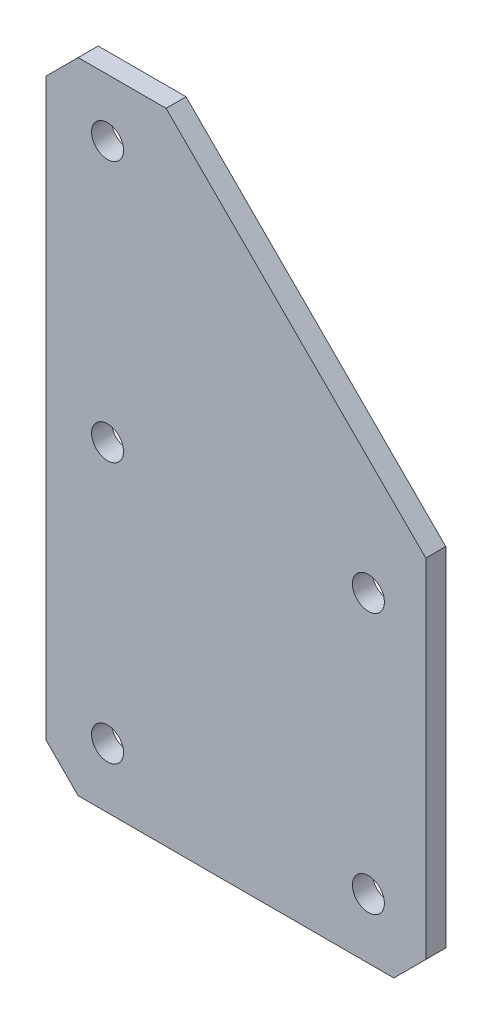
SolidWorks part; units mm, degrees
ref_plane "Front Plane" through (0, 0, 0) normal (0, 0, 1) x (1, 0, 0)
ref_plane "Top Plane" through (0, 0, 0) normal (0, 1, 0) x (1, 0, 0)
ref_plane "Right Plane" through (0, 0, 0) normal (1, 0, 0) x (0, 0, -1)
sketch "Sketch1" plane through (0, 0, 0) normal (0, 0, 1) x (1, 0, 0)
  line L0 (-95.3644, 10.476) -> (-35.0394, 10.476)
  line L3 (-35.0394, 70.801) -> (-35.0394, 10.476)
  line L4 (-95.3644, 112.076) -> (-95.3644, 10.476)
  line L5 (-95.3644, 112.076) -> (-76.3144, 112.076)
  line L6 (-35.0394, 70.801) -> (-76.3144, 112.076)
  dimension "D1" = 101.6
extrude "Boss-Extrude1" add sketch "Sketch1" along normal blind 3.175
sketch "Sketch2" plane through (0, 0, 0) normal (0, 0, -1) x (-1, 0, 0)
  line L0 (85.6171, 20.001) -> (44.1627, 20.001) construction
  line L1 (85.6171, 20.001) -> (85.6171, 61.4554) construction
  line L2 (85.6171, 61.4554) -> (85.6171, 102.9097) construction
  line L3 (44.1627, 20.001) -> (44.1627, 61.4554) construction
  line L4 (44.1627, 61.4554) -> (85.6171, 61.4554) construction
  circle A0 centre (44.1627, 20.001) radius 2.54 construction
  circle A1 centre (44.1627, 20.001) radius 2.54
  circle A2 centre (85.6171, 20.001) radius 2.54 construction
  circle A3 centre (85.6171, 20.001) radius 2.54
  circle A4 centre (85.6171, 61.4554) radius 2.54
  circle A5 centre (85.6171, 102.9097) radius 2.54
  circle A6 centre (44.1627, 61.4554) radius 2.54
extrude "Cut-Extrude1" cut sketch "Sketch2" against normal through all
chamfer "Chamfer1" distance 5.08 angle 45 3 edges at (-95.3644, 112.076, 1.5875) (-95.3644, 10.476, 1.5875) (-35.0394, 10.476, 1.5875)
